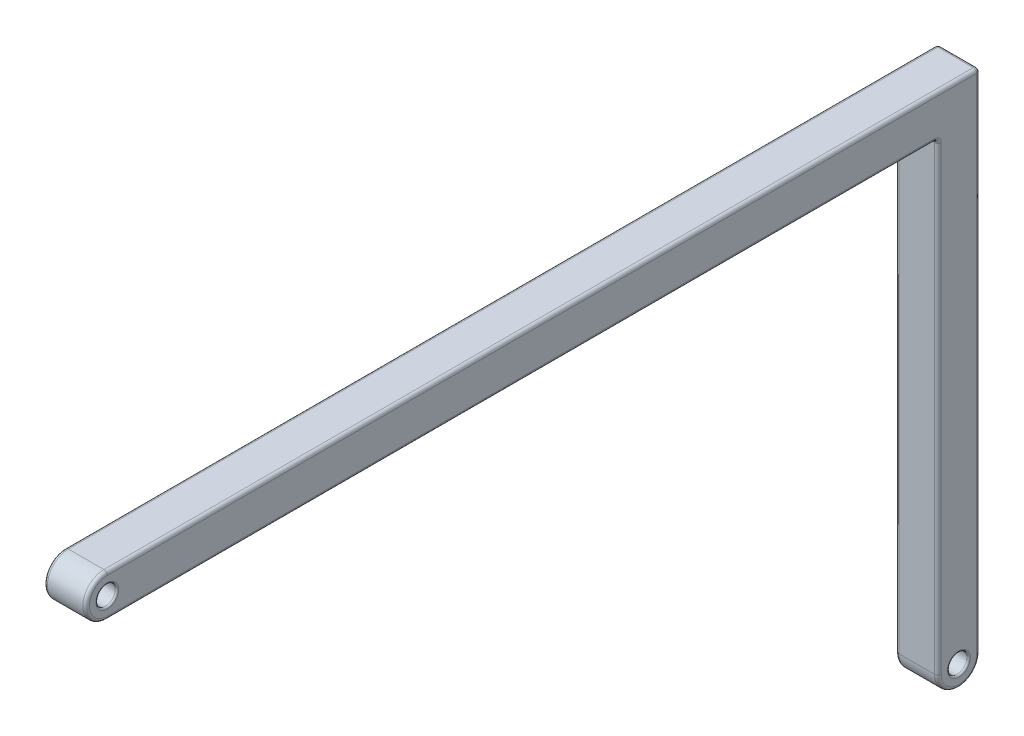
SolidWorks part; units mm, degrees
ref_plane "Front Plane" through (0, 0, 0) normal (0, 0, 1) x (1, 0, 0)
ref_plane "Top Plane" through (0, 0, 0) normal (0, 1, 0) x (1, 0, 0)
ref_plane "Right Plane" through (0, 0, 0) normal (1, 0, 0) x (0, 0, -1)
sketch "Sketch1" plane through (0, 0, 0) normal (1, 0, 0) x (0, 0, -1)
  line L1 (0, 0) -> (50.5, 0)
  line L8 (0, 0) -> (0, -2.5) construction
  line L12 (50.5, 0) -> (50.5, -2.5) construction
  line L13 (0, -2.5) -> (49.25, -2.5)
  line L16 (50.5, -1.25) -> (51.75, -1.25) construction
  line L17 (50.5, 0) -> (51.75, 0)
  line L18 (51.75, 0) -> (51.75, -30)
  line L19 (51.75, -30) -> (49.25, -30) construction
  line L20 (49.25, -30) -> (49.25, -2.5)
  circle A0 centre (0, -1.25) radius 0.575
  arc A1 (0, -2.5) -> (0, 0) centre (0, -1.25) cw
  arc A4 (49.25, -30) -> (51.75, -30) centre (50.5, -30) ccw
  circle A5 centre (50.5, -30) radius 0.575
  dimension "D1" = 1.15
  dimension "D4" = 1.25
  dimension "D3" = 50.5
  dimension "D7" = 1.15
  dimension "D2" = 2.5
  dimension "D5" = 30
  dimension "D6" = 2.5
extrude "Boss-Extrude1" add sketch "Sketch1" along normal blind 2.5
fillet "Fillet2" radius 0.1 4 edges at (0, -1.25, -0.575) (2.5, -1.25, -0.575) (0, -30, -51.075) (2.5, -30, -51.075)
fillet "Fillet3" radius 0.2 14 edges at (2.5, -2.5, -24.625) (2.5, -1.25, 1.25) (0, -2.5, -24.625) (0, -1.25, 1.25) (2.5, -15, -51.75) (2.5, -31.25, -50.5) (0, -15, -51.75) (0, -31.25, -50.5) (1.25, 0, -51.75) (2.5, 0, -25.875) (0, 0, -25.875) (1.25, -2.5, -49.25) (2.5, -16.25, -49.25) (0, -16.25, -49.25)
